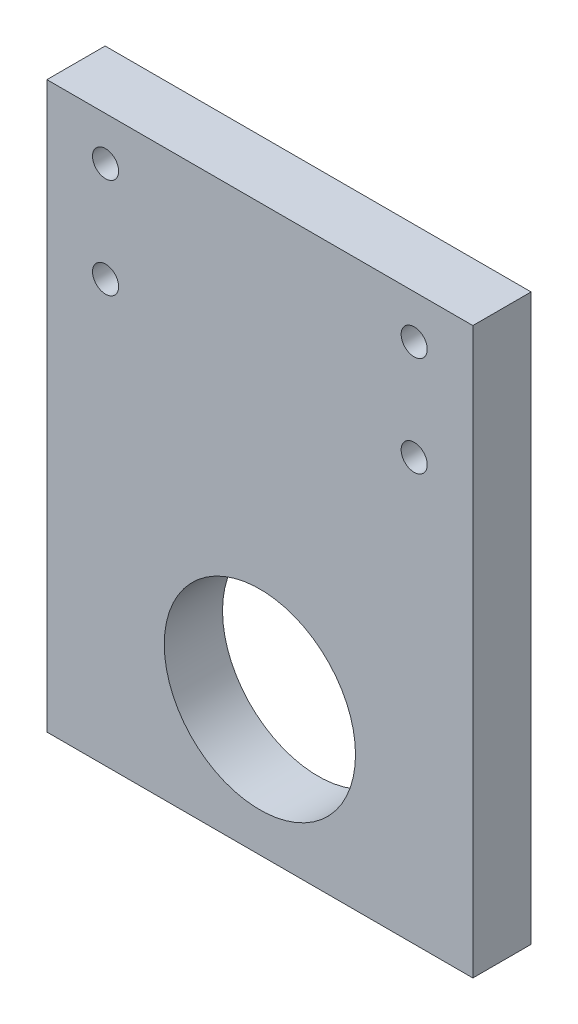
SolidWorks part; units mm, degrees
ref_plane "Front Plane" through (0, 0, 0) normal (0, 0, 1) x (1, 0, 0)
ref_plane "Top Plane" through (0, 0, 0) normal (0, 1, 0) x (1, 0, 0)
ref_plane "Right Plane" through (0, 0, 0) normal (1, 0, 0) x (0, 0, -1)
sketch "Sketch1" plane through (0, 0, 0) normal (0, 0, 1) x (1, 0, 0)
  line L1 (0, 0) -> (49, 0)
  line L2 (0, 0) -> (0, 65)
  line L3 (0, 65) -> (49, 65)
  line L4 (49, 0) -> (49, 65)
  circle A0 centre (6.75, 60) radius 1.5
  circle A1 centre (6.75, 48.5) radius 1.5
  circle A2 centre (42.25, 60) radius 1.5
  circle A3 centre (42.25, 48.5) radius 1.5
  circle A4 centre (24.5, 15.5) radius 11
  dimension "D3" = 3
  dimension "D4" = 3
  dimension "D5" = 3
  dimension "D6" = 3
  dimension "D7" = 22
  dimension "D1" = 49
  dimension "D2" = 65
  dimension "D8" = 35.5
  dimension "D9" = 35.5
  dimension "D10" = 11.5
  dimension "D11" = 5
  dimension "D12" = 6.75
  dimension "D13" = 15.5
  dimension "D14" = 24.5
extrude "Boss-Extrude1" add sketch "Sketch1" along normal blind 6.7
